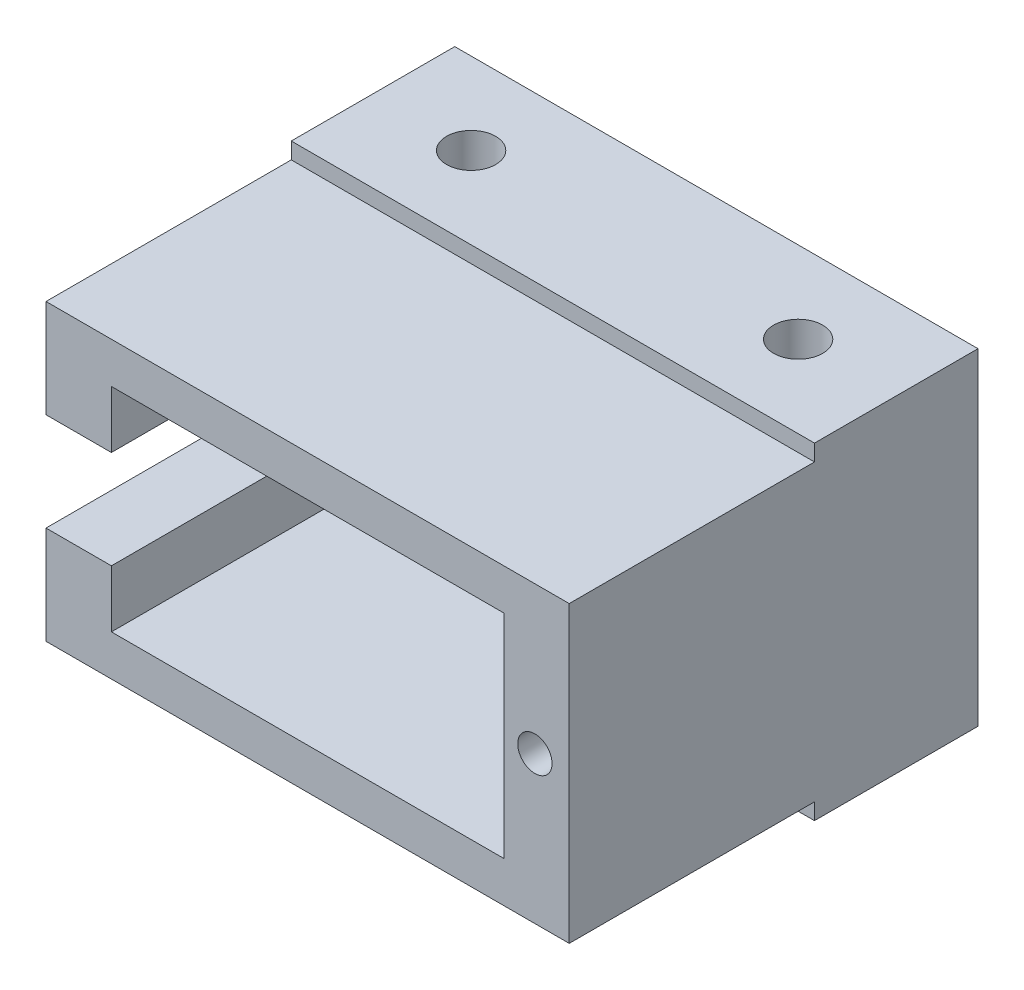
SolidWorks part; units mm, degrees
ref_plane "Plan de face" through (0, 0, 0) normal (0, 0, 1) x (1, 0, 0)
ref_plane "Plan de dessus" through (0, 0, 0) normal (0, 1, 0) x (1, 0, 0)
ref_plane "Plan de droite" through (0, 0, 0) normal (1, 0, 0) x (0, 0, -1)
sketch "Esquisse15" plane through (0, 0, 0) normal (0, 0, 1) x (1, 0, 0)
  line L1 (-16, 10) -> (16, 10)
  line L2 (-16, 10) -> (-16, -10)
  line L3 (-16, -10) -> (16, -10)
  line L4 (16, 10) -> (16, -10)
  line L5 (-16, 10) -> (16, -10) construction
  line L6 (-16, -10) -> (16, 10) construction
  point P0 (0, 0)
  dimension "D1" = 20
  dimension "D2" = 32
extrude "Boss.-Extru.1" add sketch "Esquisse15" along normal blind 10
sketch "Esquisse16" plane through (0, 0, 10) normal (0, 0, 1) x (1, 0, 0)
  line L0 (-16, 9) -> (16, 9)
  line L1 (-16, 10) -> (-16, -10) construction
  line L2 (16, -10) -> (16, 10) construction
  line L3 (16, 9) -> (16, -9)
  line L4 (16, -9) -> (-16, -9)
  line L5 (-16, -9) -> (-16, 9)
  line L6 (16, 10) -> (-16, 10) construction
  line L7 (-16, -10) -> (16, -10) construction
  line L9 (-12, 6.5) -> (12, 6.5)
  line L10 (-12, 6.5) -> (-12, -6.5)
  line L11 (-12, -6.5) -> (12, -6.5)
  line L12 (12, 6.5) -> (12, -6.5)
  line L13 (-12, 6.5) -> (12, -6.5) construction
  line L14 (-12, -6.5) -> (12, 6.5) construction
  point P12 (0, 0)
  dimension "D1" = 1
  dimension "D2" = 1
  dimension "D3" = 2.5
  dimension "D4" = 4
extrude "Boss.-Extru.2" add sketch "Esquisse16" along normal blind 15
sketch "Esquisse17" plane through (-16, 0, 0) normal (-1, 0, 0) x (0, 0, 1)
  line L0 (0, 3) -> (25, 3)
  line L1 (0, 10) -> (0, -10) construction
  line L2 (25, 3) -> (25, -3)
  line L3 (25, -3) -> (0, -3)
  line L4 (0, -3) -> (0, 3)
  point P5 (0, 0)
  dimension "D1" = 25
  dimension "D2" = 6
extrude "Enlèv. mat.-Extru.8" cut sketch "Esquisse17" against normal blind 4
sketch "Esquisse19" plane through (0, 0, 25) normal (0, 0, 1) x (1, 0, 0)
  line L5 (12, 0) -> (16, 0) construction
  line L6 (12, -6.5) -> (12, 6.5) construction
  line L7 (16, -9) -> (16, 9) construction
  line L12 (12, -6.5) -> (12, 6.5) construction
  circle A1 centre (13.9, 0) radius 1.05
  dimension "D2" = 2.1
  dimension "D4" = 1.9
extrude "Enlèv. mat.-Extru.10" cut sketch "Esquisse19" against normal blind 6
sketch "Esquisse20" plane through (0, 10, 0) normal (0, 1, 0) x (1, 0, 0)
  line L0 (-16, -5) -> (16, -5) construction
  line L1 (-16, -10) -> (-16, 0) construction
  line L2 (16, -10) -> (16, 0) construction
  circle A0 centre (-10, -5) radius 1.5
  circle A1 centre (10, -5) radius 1.5
  dimension "D1" = 3
  dimension "D2" = 3
  dimension "D3" = 6
  dimension "D4" = 6
extrude "Enlèv. mat.-Extru.11" cut sketch "Esquisse20" against normal up to next
